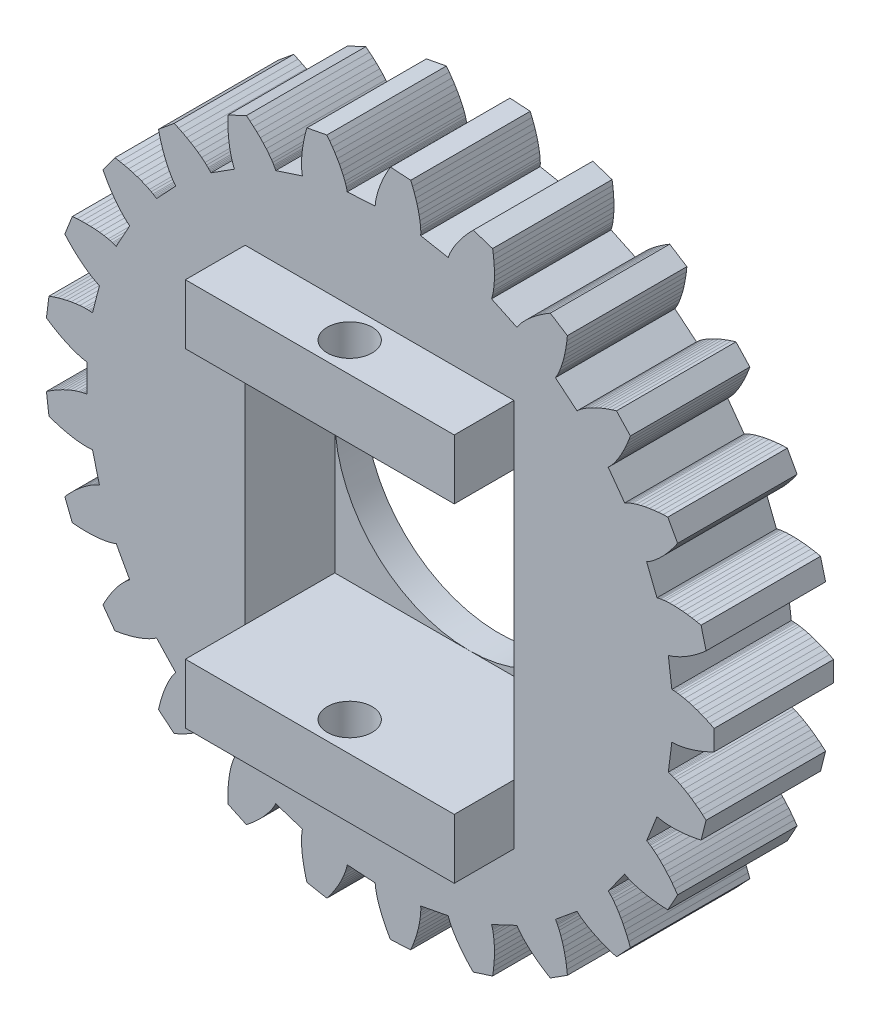
SolidWorks part; units mm, degrees
ref_plane "Front Plane" through (0, 0, 0) normal (0, 0, 1) x (1, 0, 0)
ref_plane "Top Plane" through (0, 0, 0) normal (0, 1, 0) x (1, 0, 0)
ref_plane "Right Plane" through (0, 0, 0) normal (1, 0, 0) x (0, 0, -1)
sketch "Model" plane through (0, 0, 0) normal (0, 0, 1) x (1, 0, 0)
  line L0 (22.5153, 13.4937) -> (22.5501, 13.4944)
  line L1 (22.5501, 13.4944) -> (22.5851, 13.4936)
  line L2 (22.5851, 13.4936) -> (22.6201, 13.4916)
  line L3 (22.6201, 13.4916) -> (22.6552, 13.4888)
  line L4 (22.6552, 13.4888) -> (22.7255, 13.481)
  line L5 (22.7255, 13.481) -> (22.796, 13.4706)
  line L6 (22.796, 13.4706) -> (22.9373, 13.4433)
  line L7 (22.9373, 13.4433) -> (23.079, 13.4085)
  line L8 (23.079, 13.4085) -> (23.221, 13.3669)
  line L9 (23.221, 13.3669) -> (23.363, 13.3191)
  line L10 (23.363, 13.3191) -> (23.5051, 13.2655)
  line L11 (23.5051, 13.2655) -> (23.647, 13.2062)
  line L12 (23.647, 13.2062) -> (23.7888, 13.1416)
  line L13 (23.7888, 13.1416) -> (23.9303, 13.0718)
  line L14 (23.9303, 13.0718) -> (23.9303, 12.3915)
  line L15 (23.9303, 12.3915) -> (23.7888, 12.3217)
  line L16 (23.7888, 12.3217) -> (23.647, 12.257)
  line L17 (23.647, 12.257) -> (23.5051, 12.1978)
  line L18 (23.5051, 12.1978) -> (23.363, 12.1441)
  line L19 (23.363, 12.1441) -> (23.221, 12.0963)
  line L20 (23.221, 12.0963) -> (23.079, 12.0548)
  line L21 (23.079, 12.0548) -> (22.9373, 12.0199)
  line L22 (22.9373, 12.0199) -> (22.796, 11.9927)
  line L23 (22.796, 11.9927) -> (22.7255, 11.9823)
  line L24 (22.7255, 11.9823) -> (22.6552, 11.9745)
  line L25 (22.6552, 11.9745) -> (22.6201, 11.9716)
  line L26 (22.6201, 11.9716) -> (22.5851, 11.9697)
  line L27 (22.5851, 11.9697) -> (22.5501, 11.9688)
  line L28 (22.5501, 11.9688) -> (22.5153, 11.9696)
  line L29 (22.5153, 11.9696) -> (22.3975, 11.0367)
  line L30 (22.3975, 11.0367) -> (22.4314, 11.0287)
  line L31 (22.4314, 11.0287) -> (22.465, 11.0192)
  line L32 (22.465, 11.0192) -> (22.4984, 11.0086)
  line L33 (22.4984, 11.0086) -> (22.5317, 10.9971)
  line L34 (22.5317, 10.9971) -> (22.5978, 10.9721)
  line L35 (22.5978, 10.9721) -> (22.6635, 10.9445)
  line L36 (22.6635, 10.9445) -> (22.7937, 10.8829)
  line L37 (22.7937, 10.8829) -> (22.9223, 10.8139)
  line L38 (22.9223, 10.8139) -> (23.0494, 10.7384)
  line L39 (23.0494, 10.7384) -> (23.1751, 10.6567)
  line L40 (23.1751, 10.6567) -> (23.2994, 10.5694)
  line L41 (23.2994, 10.5694) -> (23.4221, 10.4767)
  line L42 (23.4221, 10.4767) -> (23.5434, 10.3789)
  line L43 (23.5434, 10.3789) -> (23.6631, 10.2761)
  line L44 (23.6631, 10.2761) -> (23.4939, 9.6172)
  line L45 (23.4939, 9.6172) -> (23.3395, 9.5847)
  line L46 (23.3395, 9.5847) -> (23.1861, 9.5574)
  line L47 (23.1861, 9.5574) -> (23.0339, 9.5353)
  line L48 (23.0339, 9.5353) -> (22.8829, 9.5187)
  line L49 (22.8829, 9.5187) -> (22.7334, 9.5077)
  line L50 (22.7334, 9.5077) -> (22.5856, 9.5027)
  line L51 (22.5856, 9.5027) -> (22.4397, 9.5042)
  line L52 (22.4397, 9.5042) -> (22.296, 9.513)
  line L53 (22.296, 9.513) -> (22.2251, 9.5205)
  line L54 (22.2251, 9.5205) -> (22.1551, 9.5304)
  line L55 (22.1551, 9.5304) -> (22.1204, 9.5364)
  line L56 (22.1204, 9.5364) -> (22.086, 9.5432)
  line L57 (22.086, 9.5432) -> (22.0519, 9.551)
  line L58 (22.0519, 9.551) -> (22.0184, 9.5604)
  line L59 (22.0184, 9.5604) -> (21.6723, 8.6861)
  line L60 (21.6723, 8.6861) -> (21.7031, 8.67)
  line L61 (21.7031, 8.67) -> (21.7333, 8.6524)
  line L62 (21.7333, 8.6524) -> (21.7631, 8.6338)
  line L63 (21.7631, 8.6338) -> (21.7925, 8.6145)
  line L64 (21.7925, 8.6145) -> (21.8503, 8.5737)
  line L65 (21.8503, 8.5737) -> (21.9071, 8.5306)
  line L66 (21.9071, 8.5306) -> (22.0178, 8.4387)
  line L67 (22.0178, 8.4387) -> (22.1252, 8.3399)
  line L68 (22.1252, 8.3399) -> (22.2296, 8.2351)
  line L69 (22.2296, 8.2351) -> (22.331, 8.1247)
  line L70 (22.331, 8.1247) -> (22.4297, 8.0093)
  line L71 (22.4297, 8.0093) -> (22.5255, 7.889)
  line L72 (22.5255, 7.889) -> (22.6186, 7.764)
  line L73 (22.6186, 7.764) -> (22.709, 7.6347)
  line L74 (22.709, 7.6347) -> (22.3812, 7.0385)
  line L75 (22.3812, 7.0385) -> (22.2236, 7.0455)
  line L76 (22.2236, 7.0455) -> (22.0683, 7.0572)
  line L77 (22.0683, 7.0572) -> (21.9153, 7.0737)
  line L78 (21.9153, 7.0737) -> (21.765, 7.0951)
  line L79 (21.765, 7.0951) -> (21.6175, 7.1216)
  line L80 (21.6175, 7.1216) -> (21.473, 7.1536)
  line L81 (21.473, 7.1536) -> (21.3321, 7.1913)
  line L82 (21.3321, 7.1913) -> (21.1951, 7.2356)
  line L83 (21.1951, 7.2356) -> (21.1283, 7.2604)
  line L84 (21.1283, 7.2604) -> (21.0629, 7.2874)
  line L85 (21.0629, 7.2874) -> (21.0308, 7.3018)
  line L86 (21.0308, 7.3018) -> (20.9992, 7.317)
  line L87 (20.9992, 7.317) -> (20.9681, 7.3331)
  line L88 (20.9681, 7.3331) -> (20.938, 7.3505)
  line L89 (20.938, 7.3505) -> (20.3853, 6.5898)
  line L90 (20.3853, 6.5898) -> (20.4112, 6.5665)
  line L91 (20.4112, 6.5665) -> (20.4361, 6.5419)
  line L92 (20.4361, 6.5419) -> (20.4602, 6.5165)
  line L93 (20.4602, 6.5165) -> (20.4839, 6.4905)
  line L94 (20.4839, 6.4905) -> (20.5298, 6.4366)
  line L95 (20.5298, 6.4366) -> (20.574, 6.3808)
  line L96 (20.574, 6.3808) -> (20.6584, 6.2642)
  line L97 (20.6584, 6.2642) -> (20.7379, 6.1418)
  line L98 (20.7379, 6.1418) -> (20.8129, 6.0143)
  line L99 (20.8129, 6.0143) -> (20.8838, 5.8822)
  line L100 (20.8838, 5.8822) -> (20.9506, 5.7458)
  line L101 (20.9506, 5.7458) -> (21.0135, 5.6055)
  line L102 (21.0135, 5.6055) -> (21.0726, 5.4613)
  line L103 (21.0726, 5.4613) -> (21.128, 5.3136)
  line L104 (21.128, 5.3136) -> (20.6622, 4.8176)
  line L105 (20.6622, 4.8176) -> (20.5113, 4.8636)
  line L106 (20.5113, 4.8636) -> (20.3638, 4.9136)
  line L107 (20.3638, 4.9136) -> (20.2197, 4.9675)
  line L108 (20.2197, 4.9675) -> (20.0794, 5.0257)
  line L109 (20.0794, 5.0257) -> (19.9432, 5.0881)
  line L110 (19.9432, 5.0881) -> (19.8112, 5.1549)
  line L111 (19.8112, 5.1549) -> (19.6841, 5.2265)
  line L112 (19.6841, 5.2265) -> (19.5624, 5.3035)
  line L113 (19.5624, 5.3035) -> (19.5039, 5.3441)
  line L114 (19.5039, 5.3441) -> (19.4472, 5.3866)
  line L115 (19.4472, 5.3866) -> (19.4197, 5.4085)
  line L116 (19.4197, 5.4085) -> (19.3929, 5.4311)
  line L117 (19.3929, 5.4311) -> (19.3668, 5.4543)
  line L118 (19.3668, 5.4543) -> (19.3419, 5.4787)
  line L119 (19.3419, 5.4787) -> (18.6174, 4.8793)
  line L120 (18.6174, 4.8793) -> (18.6367, 4.8503)
  line L121 (18.6367, 4.8503) -> (18.6547, 4.8204)
  line L122 (18.6547, 4.8204) -> (18.6718, 4.7898)
  line L123 (18.6718, 4.7898) -> (18.6882, 4.7586)
  line L124 (18.6882, 4.7586) -> (18.7193, 4.6951)
  line L125 (18.7193, 4.6951) -> (18.7483, 4.63)
  line L126 (18.7483, 4.63) -> (18.801, 4.496)
  line L127 (18.801, 4.496) -> (18.8476, 4.3577)
  line L128 (18.8476, 4.3577) -> (18.8885, 4.2156)
  line L129 (18.8885, 4.2156) -> (18.9243, 4.07)
  line L130 (18.9243, 4.07) -> (18.9551, 3.9213)
  line L131 (18.9551, 3.9213) -> (18.9811, 3.7697)
  line L132 (18.9811, 3.7697) -> (19.0025, 3.6154)
  line L133 (19.0025, 3.6154) -> (19.0194, 3.4586)
  line L134 (19.0194, 3.4586) -> (18.445, 3.094)
  line L135 (18.445, 3.094) -> (18.3102, 3.1761)
  line L136 (18.3102, 3.1761) -> (18.1797, 3.2611)
  line L137 (18.1797, 3.2611) -> (18.0536, 3.3493)
  line L138 (18.0536, 3.3493) -> (17.9322, 3.4404)
  line L139 (17.9322, 3.4404) -> (17.8157, 3.5348)
  line L140 (17.8157, 3.5348) -> (17.7045, 3.6323)
  line L141 (17.7045, 3.6323) -> (17.5992, 3.7333)
  line L142 (17.5992, 3.7333) -> (17.5004, 3.8381)
  line L143 (17.5004, 3.8381) -> (17.4539, 3.892)
  line L144 (17.4539, 3.892) -> (17.4096, 3.9472)
  line L145 (17.4096, 3.9472) -> (17.3884, 3.9753)
  line L146 (17.3884, 3.9753) -> (17.368, 4.0038)
  line L147 (17.368, 4.0038) -> (17.3486, 4.0329)
  line L148 (17.3486, 4.0329) -> (17.3305, 4.0626)
  line L149 (17.3305, 4.0626) -> (16.4797, 3.6623)
  line L150 (16.4797, 3.6623) -> (16.4912, 3.6294)
  line L151 (16.4912, 3.6294) -> (16.5012, 3.5959)
  line L152 (16.5012, 3.5959) -> (16.5101, 3.562)
  line L153 (16.5101, 3.562) -> (16.5183, 3.5278)
  line L154 (16.5183, 3.5278) -> (16.5326, 3.4585)
  line L155 (16.5326, 3.4585) -> (16.5445, 3.3882)
  line L156 (16.5445, 3.3882) -> (16.5622, 3.2454)
  line L157 (16.5622, 3.2454) -> (16.5729, 3.0998)
  line L158 (16.5729, 3.0998) -> (16.5772, 2.952)
  line L159 (16.5772, 2.952) -> (16.5756, 2.8021)
  line L160 (16.5756, 2.8021) -> (16.5685, 2.6504)
  line L161 (16.5685, 2.6504) -> (16.556, 2.4971)
  line L162 (16.556, 2.4971) -> (16.5384, 2.3423)
  line L163 (16.5384, 2.3423) -> (16.5157, 2.1862)
  line L164 (16.5157, 2.1862) -> (15.8687, 1.9759)
  line L165 (15.8687, 1.9759) -> (15.7586, 2.0889)
  line L166 (15.7586, 2.0889) -> (15.6533, 2.2038)
  line L167 (15.6533, 2.2038) -> (15.5531, 2.3205)
  line L168 (15.5531, 2.3205) -> (15.4582, 2.439)
  line L169 (15.4582, 2.439) -> (15.3688, 2.5593)
  line L170 (15.3688, 2.5593) -> (15.2854, 2.6815)
  line L171 (15.2854, 2.6815) -> (15.2085, 2.8055)
  line L172 (15.2085, 2.8055) -> (15.1389, 2.9315)
  line L173 (15.1389, 2.9315) -> (15.1072, 2.9954)
  line L174 (15.1072, 2.9954) -> (15.078, 3.0598)
  line L175 (15.078, 3.0598) -> (15.0645, 3.0923)
  line L176 (15.0645, 3.0923) -> (15.0519, 3.125)
  line L177 (15.0519, 3.125) -> (15.0402, 3.158)
  line L178 (15.0402, 3.158) -> (15.0302, 3.1913)
  line L179 (15.0302, 3.1913) -> (14.1065, 3.0151)
  line L180 (14.1065, 3.0151) -> (14.1095, 2.9804)
  line L181 (14.1095, 2.9804) -> (14.1108, 2.9455)
  line L182 (14.1108, 2.9455) -> (14.111, 2.9104)
  line L183 (14.111, 2.9104) -> (14.1104, 2.8752)
  line L184 (14.1104, 2.8752) -> (14.107, 2.8046)
  line L185 (14.107, 2.8046) -> (14.1011, 2.7336)
  line L186 (14.1011, 2.7336) -> (14.0827, 2.5908)
  line L187 (14.0827, 2.5908) -> (14.0569, 2.4471)
  line L188 (14.0569, 2.4471) -> (14.0243, 2.3029)
  line L189 (14.0243, 2.3029) -> (13.9855, 2.1581)
  line L190 (13.9855, 2.1581) -> (13.9409, 2.0129)
  line L191 (13.9409, 2.0129) -> (13.8907, 1.8675)
  line L192 (13.8907, 1.8675) -> (13.8351, 1.722)
  line L193 (13.8351, 1.722) -> (13.7743, 1.5764)
  line L194 (13.7743, 1.5764) -> (13.0953, 1.5337)
  line L195 (13.0953, 1.5337) -> (13.0168, 1.6705)
  line L196 (13.0168, 1.6705) -> (12.9434, 1.808)
  line L197 (12.9434, 1.808) -> (12.8753, 1.9459)
  line L198 (12.8753, 1.9459) -> (12.8128, 2.0843)
  line L199 (12.8128, 2.0843) -> (12.7562, 2.2231)
  line L200 (12.7562, 2.2231) -> (12.7058, 2.3621)
  line L201 (12.7058, 2.3621) -> (12.6622, 2.5014)
  line L202 (12.6622, 2.5014) -> (12.6261, 2.6408)
  line L203 (12.6261, 2.6408) -> (12.6113, 2.7105)
  line L204 (12.6113, 2.7105) -> (12.599, 2.7801)
  line L205 (12.599, 2.7801) -> (12.594, 2.815)
  line L206 (12.594, 2.815) -> (12.5899, 2.8498)
  line L207 (12.5899, 2.8498) -> (12.5868, 2.8846)
  line L208 (12.5868, 2.8846) -> (12.5854, 2.9194)
  line L209 (12.5854, 2.9194) -> (11.6469, 2.9784)
  line L210 (11.6469, 2.9784) -> (11.6411, 2.9441)
  line L211 (11.6411, 2.9441) -> (11.6337, 2.91)
  line L212 (11.6337, 2.91) -> (11.6253, 2.8759)
  line L213 (11.6253, 2.8759) -> (11.6159, 2.842)
  line L214 (11.6159, 2.842) -> (11.595, 2.7744)
  line L215 (11.595, 2.7744) -> (11.5716, 2.7071)
  line L216 (11.5716, 2.7071) -> (11.5184, 2.5733)
  line L217 (11.5184, 2.5733) -> (11.4576, 2.4407)
  line L218 (11.4576, 2.4407) -> (11.3902, 2.309)
  line L219 (11.3902, 2.309) -> (11.3166, 2.1784)
  line L220 (11.3166, 2.1784) -> (11.2372, 2.049)
  line L221 (11.2372, 2.049) -> (11.1525, 1.9206)
  line L222 (11.1525, 1.9206) -> (11.0624, 1.7935)
  line L223 (11.0624, 1.7935) -> (10.9673, 1.6676)
  line L224 (10.9673, 1.6676) -> (10.2991, 1.7951)
  line L225 (10.2991, 1.7951) -> (10.257, 1.9471)
  line L226 (10.257, 1.9471) -> (10.2201, 2.0985)
  line L227 (10.2201, 2.0985) -> (10.1885, 2.249)
  line L228 (10.1885, 2.249) -> (10.1624, 2.3986)
  line L229 (10.1624, 2.3986) -> (10.1421, 2.5471)
  line L230 (10.1421, 2.5471) -> (10.1278, 2.6943)
  line L231 (10.1278, 2.6943) -> (10.1202, 2.8401)
  line L232 (10.1202, 2.8401) -> (10.1199, 2.984)
  line L233 (10.1199, 2.984) -> (10.1229, 3.0552)
  line L234 (10.1229, 3.0552) -> (10.1284, 3.1258)
  line L235 (10.1284, 3.1258) -> (10.1322, 3.1607)
  line L236 (10.1322, 3.1607) -> (10.1368, 3.1955)
  line L237 (10.1368, 3.1955) -> (10.1425, 3.23)
  line L238 (10.1425, 3.23) -> (10.1498, 3.264)
  line L239 (10.1498, 3.264) -> (9.2555, 3.5546)
  line L240 (9.2555, 3.5546) -> (9.2413, 3.5228)
  line L241 (9.2413, 3.5228) -> (9.2257, 3.4916)
  line L242 (9.2257, 3.4916) -> (9.209, 3.4607)
  line L243 (9.209, 3.4607) -> (9.1915, 3.4302)
  line L244 (9.1915, 3.4302) -> (9.1545, 3.3699)
  line L245 (9.1545, 3.3699) -> (9.1151, 3.3105)
  line L246 (9.1151, 3.3105) -> (9.0302, 3.1942)
  line L247 (9.0302, 3.1942) -> (8.9384, 3.0808)
  line L248 (8.9384, 3.0808) -> (8.8403, 2.9701)
  line L249 (8.8403, 2.9701) -> (8.7366, 2.8619)
  line L250 (8.7366, 2.8619) -> (8.6275, 2.7562)
  line L251 (8.6275, 2.7562) -> (8.5135, 2.653)
  line L252 (8.5135, 2.653) -> (8.3947, 2.5522)
  line L253 (8.3947, 2.5522) -> (8.2713, 2.4539)
  line L254 (8.2713, 2.4539) -> (7.6557, 2.7436)
  line L255 (7.6557, 2.7436) -> (7.6528, 2.9013)
  line L256 (7.6528, 2.9013) -> (7.6547, 3.0571)
  line L257 (7.6547, 3.0571) -> (7.6615, 3.2108)
  line L258 (7.6615, 3.2108) -> (7.6734, 3.3622)
  line L259 (7.6734, 3.3622) -> (7.6906, 3.5111)
  line L260 (7.6906, 3.5111) -> (7.7135, 3.6572)
  line L261 (7.7135, 3.6572) -> (7.7423, 3.8003)
  line L262 (7.7423, 3.8003) -> (7.7778, 3.9398)
  line L263 (7.7778, 3.9398) -> (7.7984, 4.008)
  line L264 (7.7984, 4.008) -> (7.8213, 4.0749)
  line L265 (7.8213, 4.0749) -> (7.8337, 4.1079)
  line L266 (7.8337, 4.1079) -> (7.8468, 4.1404)
  line L267 (7.8468, 4.1404) -> (7.8609, 4.1724)
  line L268 (7.8609, 4.1724) -> (7.8764, 4.2036)
  line L269 (7.8764, 4.2036) -> (7.0825, 4.7074)
  line L270 (7.0825, 4.7074) -> (7.0608, 4.6801)
  line L271 (7.0608, 4.6801) -> (7.0379, 4.6537)
  line L272 (7.0379, 4.6537) -> (7.0141, 4.628)
  line L273 (7.0141, 4.628) -> (6.9896, 4.6028)
  line L274 (6.9896, 4.6028) -> (6.9387, 4.5536)
  line L275 (6.9387, 4.5536) -> (6.8858, 4.5059)
  line L276 (6.8858, 4.5059) -> (6.7746, 4.4144)
  line L277 (6.7746, 4.4144) -> (6.6575, 4.3274)
  line L278 (6.6575, 4.3274) -> (6.535, 4.2445)
  line L279 (6.535, 4.2445) -> (6.4076, 4.1655)
  line L280 (6.4076, 4.1655) -> (6.2757, 4.0903)
  line L281 (6.2757, 4.0903) -> (6.1395, 4.0186)
  line L282 (6.1395, 4.0186) -> (5.9994, 3.9506)
  line L283 (5.9994, 3.9506) -> (5.8554, 3.8861)
  line L284 (5.8554, 3.8861) -> (5.3312, 4.3197)
  line L285 (5.3312, 4.3197) -> (5.3676, 4.4732)
  line L286 (5.3676, 4.4732) -> (5.4082, 4.6237)
  line L287 (5.4082, 4.6237) -> (5.453, 4.7708)
  line L288 (5.453, 4.7708) -> (5.5022, 4.9145)
  line L289 (5.5022, 4.9145) -> (5.556, 5.0544)
  line L290 (5.556, 5.0544) -> (5.6144, 5.1903)
  line L291 (5.6144, 5.1903) -> (5.6779, 5.3217)
  line L292 (5.6779, 5.3217) -> (5.747, 5.4479)
  line L293 (5.747, 5.4479) -> (5.7839, 5.5089)
  line L294 (5.7839, 5.5089) -> (5.8227, 5.5681)
  line L295 (5.8227, 5.5681) -> (5.8429, 5.5969)
  line L296 (5.8429, 5.5969) -> (5.8637, 5.6251)
  line L297 (5.8637, 5.6251) -> (5.8853, 5.6526)
  line L298 (5.8853, 5.6526) -> (5.9081, 5.6789)
  line L299 (5.9081, 5.6789) -> (5.2644, 6.3644)
  line L300 (5.2644, 6.3644) -> (5.2367, 6.3433)
  line L301 (5.2367, 6.3433) -> (5.2079, 6.3235)
  line L302 (5.2079, 6.3235) -> (5.1784, 6.3045)
  line L303 (5.1784, 6.3045) -> (5.1484, 6.2862)
  line L304 (5.1484, 6.2862) -> (5.0869, 6.2512)
  line L305 (5.0869, 6.2512) -> (5.0238, 6.2181)
  line L306 (5.0238, 6.2181) -> (4.8934, 6.1571)
  line L307 (4.8934, 6.1571) -> (4.7583, 6.102)
  line L308 (4.7583, 6.102) -> (4.619, 6.0522)
  line L309 (4.619, 6.0522) -> (4.476, 6.0074)
  line L310 (4.476, 6.0074) -> (4.3295, 5.9673)
  line L311 (4.3295, 5.9673) -> (4.1798, 5.9318)
  line L312 (4.1798, 5.9318) -> (4.0272, 5.9007)
  line L313 (4.0272, 5.9007) -> (3.8717, 5.874)
  line L314 (3.8717, 5.874) -> (3.4718, 6.4244)
  line L315 (3.4718, 6.4244) -> (3.5452, 6.5641)
  line L316 (3.5452, 6.5641) -> (3.6219, 6.6996)
  line L317 (3.6219, 6.6996) -> (3.7019, 6.831)
  line L318 (3.7019, 6.831) -> (3.7853, 6.9579)
  line L319 (3.7853, 6.9579) -> (3.8721, 7.0801)
  line L320 (3.8721, 7.0801) -> (3.9625, 7.1972)
  line L321 (3.9625, 7.1972) -> (4.0567, 7.3086)
  line L322 (4.0567, 7.3086) -> (4.1551, 7.4138)
  line L323 (4.1551, 7.4138) -> (4.206, 7.4636)
  line L324 (4.206, 7.4636) -> (4.2583, 7.5113)
  line L325 (4.2583, 7.5113) -> (4.285, 7.5342)
  line L326 (4.285, 7.5342) -> (4.3122, 7.5563)
  line L327 (4.3122, 7.5563) -> (4.3399, 7.5776)
  line L328 (4.3399, 7.5776) -> (4.3685, 7.5975)
  line L329 (4.3685, 7.5975) -> (3.9155, 8.4215)
  line L330 (3.9155, 8.4215) -> (3.8834, 8.4079)
  line L331 (3.8834, 8.4079) -> (3.8506, 8.3959)
  line L332 (3.8506, 8.3959) -> (3.8174, 8.3848)
  line L333 (3.8174, 8.3848) -> (3.7837, 8.3745)
  line L334 (3.7837, 8.3745) -> (3.7154, 8.3559)
  line L335 (3.7154, 8.3559) -> (3.6461, 8.3396)
  line L336 (3.6461, 8.3396) -> (3.5046, 8.3129)
  line L337 (3.5046, 8.3129) -> (3.36, 8.2932)
  line L338 (3.36, 8.2932) -> (3.2127, 8.2796)
  line L339 (3.2127, 8.2796) -> (3.0631, 8.2717)
  line L340 (3.0631, 8.2717) -> (2.9112, 8.2693)
  line L341 (2.9112, 8.2693) -> (2.7574, 8.2721)
  line L342 (2.7574, 8.2721) -> (2.6018, 8.28)
  line L343 (2.6018, 8.28) -> (2.4446, 8.2928)
  line L344 (2.4446, 8.2928) -> (2.1941, 8.9254)
  line L345 (2.1941, 8.9254) -> (2.3, 9.0424)
  line L346 (2.3, 9.0424) -> (2.408, 9.1547)
  line L347 (2.408, 9.1547) -> (2.5182, 9.262)
  line L348 (2.5182, 9.262) -> (2.6305, 9.3642)
  line L349 (2.6305, 9.3642) -> (2.745, 9.4609)
  line L350 (2.745, 9.4609) -> (2.8617, 9.5518)
  line L351 (2.8617, 9.5518) -> (2.9806, 9.6364)
  line L352 (2.9806, 9.6364) -> (3.102, 9.7138)
  line L353 (3.102, 9.7138) -> (3.1637, 9.7494)
  line L354 (3.1637, 9.7494) -> (3.2262, 9.7825)
  line L355 (3.2262, 9.7825) -> (3.2578, 9.7981)
  line L356 (3.2578, 9.7981) -> (3.2897, 9.8128)
  line L357 (3.2897, 9.8128) -> (3.3218, 9.8265)
  line L358 (3.3218, 9.8265) -> (3.3544, 9.8386)
  line L359 (3.3544, 9.8386) -> (3.1206, 10.7493)
  line L360 (3.1206, 10.7493) -> (3.0862, 10.7442)
  line L361 (3.0862, 10.7442) -> (3.0514, 10.7407)
  line L362 (3.0514, 10.7407) -> (3.0164, 10.7383)
  line L363 (3.0164, 10.7383) -> (2.9813, 10.7367)
  line L364 (2.9813, 10.7367) -> (2.9105, 10.7356)
  line L365 (2.9105, 10.7356) -> (2.8393, 10.7371)
  line L366 (2.8393, 10.7371) -> (2.6956, 10.7464)
  line L367 (2.6956, 10.7464) -> (2.5506, 10.7632)
  line L368 (2.5506, 10.7632) -> (2.4046, 10.7867)
  line L369 (2.4046, 10.7867) -> (2.2577, 10.8163)
  line L370 (2.2577, 10.8163) -> (2.11, 10.8517)
  line L371 (2.11, 10.8517) -> (1.9618, 10.8927)
  line L372 (1.9618, 10.8927) -> (1.813, 10.9391)
  line L373 (1.813, 10.9391) -> (1.6639, 10.9906)
  line L374 (1.6639, 10.9906) -> (1.5786, 11.6655)
  line L375 (1.5786, 11.6655) -> (1.7103, 11.7525)
  line L376 (1.7103, 11.7525) -> (1.8428, 11.8344)
  line L377 (1.8428, 11.8344) -> (1.9762, 11.911)
  line L378 (1.9762, 11.911) -> (2.1104, 11.982)
  line L379 (2.1104, 11.982) -> (2.2454, 12.0472)
  line L380 (2.2454, 12.0472) -> (2.381, 12.1063)
  line L381 (2.381, 12.1063) -> (2.5172, 12.1586)
  line L382 (2.5172, 12.1586) -> (2.654, 12.2034)
  line L383 (2.654, 12.2034) -> (2.7227, 12.2225)
  line L384 (2.7227, 12.2225) -> (2.7915, 12.2391)
  line L385 (2.7915, 12.2391) -> (2.8259, 12.2463)
  line L386 (2.8259, 12.2463) -> (2.8604, 12.2526)
  line L387 (2.8604, 12.2526) -> (2.8949, 12.2578)
  line L388 (2.8949, 12.2578) -> (2.9296, 12.2615)
  line L389 (2.9296, 12.2615) -> (2.9296, 13.2018)
  line L390 (2.9296, 13.2018) -> (2.8949, 13.2054)
  line L391 (2.8949, 13.2054) -> (2.8604, 13.2107)
  line L392 (2.8604, 13.2107) -> (2.8259, 13.217)
  line L393 (2.8259, 13.217) -> (2.7915, 13.2242)
  line L394 (2.7915, 13.2242) -> (2.7227, 13.2408)
  line L395 (2.7227, 13.2408) -> (2.654, 13.2599)
  line L396 (2.654, 13.2599) -> (2.5172, 13.3047)
  line L397 (2.5172, 13.3047) -> (2.381, 13.357)
  line L398 (2.381, 13.357) -> (2.2454, 13.416)
  line L399 (2.2454, 13.416) -> (2.1104, 13.4812)
  line L400 (2.1104, 13.4812) -> (1.9762, 13.5523)
  line L401 (1.9762, 13.5523) -> (1.8428, 13.6289)
  line L402 (1.8428, 13.6289) -> (1.7103, 13.7107)
  line L403 (1.7103, 13.7107) -> (1.5786, 13.7977)
  line L404 (1.5786, 13.7977) -> (1.6639, 14.4727)
  line L405 (1.6639, 14.4727) -> (1.813, 14.5242)
  line L406 (1.813, 14.5242) -> (1.9618, 14.5705)
  line L407 (1.9618, 14.5705) -> (2.11, 14.6115)
  line L408 (2.11, 14.6115) -> (2.2577, 14.647)
  line L409 (2.2577, 14.647) -> (2.4046, 14.6766)
  line L410 (2.4046, 14.6766) -> (2.5506, 14.7)
  line L411 (2.5506, 14.7) -> (2.6956, 14.7168)
  line L412 (2.6956, 14.7168) -> (2.8393, 14.7261)
  line L413 (2.8393, 14.7261) -> (2.9105, 14.7276)
  line L414 (2.9105, 14.7276) -> (2.9813, 14.7266)
  line L415 (2.9813, 14.7266) -> (3.0164, 14.725)
  line L416 (3.0164, 14.725) -> (3.0514, 14.7225)
  line L417 (3.0514, 14.7225) -> (3.0862, 14.719)
  line L418 (3.0862, 14.719) -> (3.1206, 14.7139)
  line L419 (3.1206, 14.7139) -> (3.3544, 15.6247)
  line L420 (3.3544, 15.6247) -> (3.3218, 15.6368)
  line L421 (3.3218, 15.6368) -> (3.2897, 15.6505)
  line L422 (3.2897, 15.6505) -> (3.2578, 15.6652)
  line L423 (3.2578, 15.6652) -> (3.2262, 15.6807)
  line L424 (3.2262, 15.6807) -> (3.1637, 15.7139)
  line L425 (3.1637, 15.7139) -> (3.102, 15.7495)
  line L426 (3.102, 15.7495) -> (2.9806, 15.8269)
  line L427 (2.9806, 15.8269) -> (2.8617, 15.9114)
  line L428 (2.8617, 15.9114) -> (2.745, 16.0023)
  line L429 (2.745, 16.0023) -> (2.6305, 16.0991)
  line L430 (2.6305, 16.0991) -> (2.5182, 16.2013)
  line L431 (2.5182, 16.2013) -> (2.408, 16.3086)
  line L432 (2.408, 16.3086) -> (2.3, 16.4209)
  line L433 (2.3, 16.4209) -> (2.1941, 16.5379)
  line L434 (2.1941, 16.5379) -> (2.4446, 17.1704)
  line L435 (2.4446, 17.1704) -> (2.6018, 17.1832)
  line L436 (2.6018, 17.1832) -> (2.7574, 17.1911)
  line L437 (2.7574, 17.1911) -> (2.9112, 17.1939)
  line L438 (2.9112, 17.1939) -> (3.0631, 17.1915)
  line L439 (3.0631, 17.1915) -> (3.2127, 17.1837)
  line L440 (3.2127, 17.1837) -> (3.36, 17.1701)
  line L441 (3.36, 17.1701) -> (3.5046, 17.1503)
  line L442 (3.5046, 17.1503) -> (3.6461, 17.1236)
  line L443 (3.6461, 17.1236) -> (3.7154, 17.1073)
  line L444 (3.7154, 17.1073) -> (3.7837, 17.0887)
  line L445 (3.7837, 17.0887) -> (3.8174, 17.0784)
  line L446 (3.8174, 17.0784) -> (3.8506, 17.0674)
  line L447 (3.8506, 17.0674) -> (3.8834, 17.0553)
  line L448 (3.8834, 17.0553) -> (3.9155, 17.0418)
  line L449 (3.9155, 17.0418) -> (4.3685, 17.8658)
  line L450 (4.3685, 17.8658) -> (4.3399, 17.8857)
  line L451 (4.3399, 17.8857) -> (4.3122, 17.9069)
  line L452 (4.3122, 17.9069) -> (4.285, 17.9291)
  line L453 (4.285, 17.9291) -> (4.2583, 17.952)
  line L454 (4.2583, 17.952) -> (4.206, 17.9996)
  line L455 (4.206, 17.9996) -> (4.1551, 18.0495)
  line L456 (4.1551, 18.0495) -> (4.0567, 18.1546)
  line L457 (4.0567, 18.1546) -> (3.9625, 18.2661)
  line L458 (3.9625, 18.2661) -> (3.8721, 18.3831)
  line L459 (3.8721, 18.3831) -> (3.7853, 18.5053)
  line L460 (3.7853, 18.5053) -> (3.7019, 18.6322)
  line L461 (3.7019, 18.6322) -> (3.6219, 18.7636)
  line L462 (3.6219, 18.7636) -> (3.5452, 18.8992)
  line L463 (3.5452, 18.8992) -> (3.4718, 19.0388)
  line L464 (3.4718, 19.0388) -> (3.8717, 19.5892)
  line L465 (3.8717, 19.5892) -> (4.0272, 19.5626)
  line L466 (4.0272, 19.5626) -> (4.1798, 19.5315)
  line L467 (4.1798, 19.5315) -> (4.3295, 19.496)
  line L468 (4.3295, 19.496) -> (4.476, 19.4559)
  line L469 (4.476, 19.4559) -> (4.619, 19.4111)
  line L470 (4.619, 19.4111) -> (4.7583, 19.3613)
  line L471 (4.7583, 19.3613) -> (4.8934, 19.3062)
  line L472 (4.8934, 19.3062) -> (5.0238, 19.2451)
  line L473 (5.0238, 19.2451) -> (5.0869, 19.2121)
  line L474 (5.0869, 19.2121) -> (5.1484, 19.1771)
  line L475 (5.1484, 19.1771) -> (5.1784, 19.1588)
  line L476 (5.1784, 19.1588) -> (5.2079, 19.1398)
  line L477 (5.2079, 19.1398) -> (5.2367, 19.1199)
  line L478 (5.2367, 19.1199) -> (5.2644, 19.0989)
  line L479 (5.2644, 19.0989) -> (5.9081, 19.7843)
  line L480 (5.9081, 19.7843) -> (5.8853, 19.8107)
  line L481 (5.8853, 19.8107) -> (5.8637, 19.8381)
  line L482 (5.8637, 19.8381) -> (5.8429, 19.8664)
  line L483 (5.8429, 19.8664) -> (5.8227, 19.8952)
  line L484 (5.8227, 19.8952) -> (5.7839, 19.9544)
  line L485 (5.7839, 19.9544) -> (5.747, 20.0153)
  line L486 (5.747, 20.0153) -> (5.6779, 20.1416)
  line L487 (5.6779, 20.1416) -> (5.6144, 20.273)
  line L488 (5.6144, 20.273) -> (5.556, 20.4089)
  line L489 (5.556, 20.4089) -> (5.5022, 20.5488)
  line L490 (5.5022, 20.5488) -> (5.453, 20.6925)
  line L491 (5.453, 20.6925) -> (5.4082, 20.8396)
  line L492 (5.4082, 20.8396) -> (5.3676, 20.99)
  line L493 (5.3676, 20.99) -> (5.3312, 21.1435)
  line L494 (5.3312, 21.1435) -> (5.8554, 21.5772)
  line L495 (5.8554, 21.5772) -> (5.9994, 21.5127)
  line L496 (5.9994, 21.5127) -> (6.1395, 21.4446)
  line L497 (6.1395, 21.4446) -> (6.2757, 21.373)
  line L498 (6.2757, 21.373) -> (6.4076, 21.2977)
  line L499 (6.4076, 21.2977) -> (6.535, 21.2188)
  line L500 (6.535, 21.2188) -> (6.6575, 21.1359)
  line L501 (6.6575, 21.1359) -> (6.7746, 21.0489)
  line L502 (6.7746, 21.0489) -> (6.8858, 20.9574)
  line L503 (6.8858, 20.9574) -> (6.9387, 20.9097)
  line L504 (6.9387, 20.9097) -> (6.9896, 20.8605)
  line L505 (6.9896, 20.8605) -> (7.0141, 20.8352)
  line L506 (7.0141, 20.8352) -> (7.0379, 20.8095)
  line L507 (7.0379, 20.8095) -> (7.0608, 20.7831)
  line L508 (7.0608, 20.7831) -> (7.0825, 20.7559)
  line L509 (7.0825, 20.7559) -> (7.8764, 21.2597)
  line L510 (7.8764, 21.2597) -> (7.8609, 21.2909)
  line L511 (7.8609, 21.2909) -> (7.8468, 21.3229)
  line L512 (7.8468, 21.3229) -> (7.8337, 21.3554)
  line L513 (7.8337, 21.3554) -> (7.8213, 21.3883)
  line L514 (7.8213, 21.3883) -> (7.7984, 21.4553)
  line L515 (7.7984, 21.4553) -> (7.7778, 21.5235)
  line L516 (7.7778, 21.5235) -> (7.7423, 21.663)
  line L517 (7.7423, 21.663) -> (7.7135, 21.806)
  line L518 (7.7135, 21.806) -> (7.6906, 21.9522)
  line L519 (7.6906, 21.9522) -> (7.6734, 22.1011)
  line L520 (7.6734, 22.1011) -> (7.6615, 22.2525)
  line L521 (7.6615, 22.2525) -> (7.6547, 22.4061)
  line L522 (7.6547, 22.4061) -> (7.6528, 22.5619)
  line L523 (7.6528, 22.5619) -> (7.6557, 22.7196)
  line L524 (7.6557, 22.7196) -> (8.2713, 23.0093)
  line L525 (8.2713, 23.0093) -> (8.3947, 22.911)
  line L526 (8.3947, 22.911) -> (8.5135, 22.8103)
  line L527 (8.5135, 22.8103) -> (8.6275, 22.707)
  line L528 (8.6275, 22.707) -> (8.7366, 22.6013)
  line L529 (8.7366, 22.6013) -> (8.8403, 22.4932)
  line L530 (8.8403, 22.4932) -> (8.9384, 22.3824)
  line L531 (8.9384, 22.3824) -> (9.0302, 22.269)
  line L532 (9.0302, 22.269) -> (9.1151, 22.1527)
  line L533 (9.1151, 22.1527) -> (9.1545, 22.0934)
  line L534 (9.1545, 22.0934) -> (9.1915, 22.0331)
  line L535 (9.1915, 22.0331) -> (9.209, 22.0026)
  line L536 (9.209, 22.0026) -> (9.2257, 21.9717)
  line L537 (9.2257, 21.9717) -> (9.2413, 21.9405)
  line L538 (9.2413, 21.9405) -> (9.2555, 21.9086)
  line L539 (9.2555, 21.9086) -> (10.1498, 22.1992)
  line L540 (10.1498, 22.1992) -> (10.1425, 22.2333)
  line L541 (10.1425, 22.2333) -> (10.1368, 22.2677)
  line L542 (10.1368, 22.2677) -> (10.1322, 22.3025)
  line L543 (10.1322, 22.3025) -> (10.1284, 22.3375)
  line L544 (10.1284, 22.3375) -> (10.1229, 22.408)
  line L545 (10.1229, 22.408) -> (10.1199, 22.4792)
  line L546 (10.1199, 22.4792) -> (10.1202, 22.6232)
  line L547 (10.1202, 22.6232) -> (10.1278, 22.7689)
  line L548 (10.1278, 22.7689) -> (10.1421, 22.9161)
  line L549 (10.1421, 22.9161) -> (10.1624, 23.0646)
  line L550 (10.1624, 23.0646) -> (10.1885, 23.2142)
  line L551 (10.1885, 23.2142) -> (10.2201, 23.3648)
  line L552 (10.2201, 23.3648) -> (10.257, 23.5161)
  line L553 (10.257, 23.5161) -> (10.2991, 23.6682)
  line L554 (10.2991, 23.6682) -> (10.9673, 23.7957)
  line L555 (10.9673, 23.7957) -> (11.0624, 23.6698)
  line L556 (11.0624, 23.6698) -> (11.1525, 23.5426)
  line L557 (11.1525, 23.5426) -> (11.2372, 23.4143)
  line L558 (11.2372, 23.4143) -> (11.3166, 23.2848)
  line L559 (11.3166, 23.2848) -> (11.3902, 23.1542)
  line L560 (11.3902, 23.1542) -> (11.4576, 23.0226)
  line L561 (11.4576, 23.0226) -> (11.5184, 22.8899)
  line L562 (11.5184, 22.8899) -> (11.5716, 22.7562)
  line L563 (11.5716, 22.7562) -> (11.595, 22.6889)
  line L564 (11.595, 22.6889) -> (11.6159, 22.6213)
  line L565 (11.6159, 22.6213) -> (11.6253, 22.5873)
  line L566 (11.6253, 22.5873) -> (11.6337, 22.5533)
  line L567 (11.6337, 22.5533) -> (11.6411, 22.5191)
  line L568 (11.6411, 22.5191) -> (11.6469, 22.4848)
  line L569 (11.6469, 22.4848) -> (12.5854, 22.5439)
  line L570 (12.5854, 22.5439) -> (12.5868, 22.5786)
  line L571 (12.5868, 22.5786) -> (12.5899, 22.6135)
  line L572 (12.5899, 22.6135) -> (12.594, 22.6483)
  line L573 (12.594, 22.6483) -> (12.599, 22.6831)
  line L574 (12.599, 22.6831) -> (12.6113, 22.7528)
  line L575 (12.6113, 22.7528) -> (12.6261, 22.8225)
  line L576 (12.6261, 22.8225) -> (12.6622, 22.9619)
  line L577 (12.6622, 22.9619) -> (12.7058, 23.1011)
  line L578 (12.7058, 23.1011) -> (12.7562, 23.2402)
  line L579 (12.7562, 23.2402) -> (12.8128, 23.3789)
  line L580 (12.8128, 23.3789) -> (12.8753, 23.5174)
  line L581 (12.8753, 23.5174) -> (12.9434, 23.6553)
  line L582 (12.9434, 23.6553) -> (13.0168, 23.7927)
  line L583 (13.0168, 23.7927) -> (13.0953, 23.9296)
  line L584 (13.0953, 23.9296) -> (13.7743, 23.8868)
  line L585 (13.7743, 23.8868) -> (13.8351, 23.7412)
  line L586 (13.8351, 23.7412) -> (13.8907, 23.5957)
  line L587 (13.8907, 23.5957) -> (13.9409, 23.4503)
  line L588 (13.9409, 23.4503) -> (13.9855, 23.3052)
  line L589 (13.9855, 23.3052) -> (14.0243, 23.1604)
  line L590 (14.0243, 23.1604) -> (14.0569, 23.0161)
  line L591 (14.0569, 23.0161) -> (14.0827, 22.8725)
  line L592 (14.0827, 22.8725) -> (14.1011, 22.7297)
  line L593 (14.1011, 22.7297) -> (14.107, 22.6587)
  line L594 (14.107, 22.6587) -> (14.1104, 22.588)
  line L595 (14.1104, 22.588) -> (14.111, 22.5528)
  line L596 (14.111, 22.5528) -> (14.1108, 22.5178)
  line L597 (14.1108, 22.5178) -> (14.1095, 22.4828)
  line L598 (14.1095, 22.4828) -> (14.1065, 22.4482)
  line L599 (14.1065, 22.4482) -> (15.0302, 22.272)
  line L600 (15.0302, 22.272) -> (15.0402, 22.3053)
  line L601 (15.0402, 22.3053) -> (15.0519, 22.3382)
  line L602 (15.0519, 22.3382) -> (15.0645, 22.3709)
  line L603 (15.0645, 22.3709) -> (15.078, 22.4034)
  line L604 (15.078, 22.4034) -> (15.1072, 22.4679)
  line L605 (15.1072, 22.4679) -> (15.1389, 22.5317)
  line L606 (15.1389, 22.5317) -> (15.2085, 22.6577)
  line L607 (15.2085, 22.6577) -> (15.2854, 22.7818)
  line L608 (15.2854, 22.7818) -> (15.3688, 22.9039)
  line L609 (15.3688, 22.9039) -> (15.4582, 23.0242)
  line L610 (15.4582, 23.0242) -> (15.5531, 23.1428)
  line L611 (15.5531, 23.1428) -> (15.6533, 23.2595)
  line L612 (15.6533, 23.2595) -> (15.7586, 23.3743)
  line L613 (15.7586, 23.3743) -> (15.8687, 23.4873)
  line L614 (15.8687, 23.4873) -> (16.5157, 23.2771)
  line L615 (16.5157, 23.2771) -> (16.5384, 23.1209)
  line L616 (16.5384, 23.1209) -> (16.556, 22.9662)
  line L617 (16.556, 22.9662) -> (16.5685, 22.8128)
  line L618 (16.5685, 22.8128) -> (16.5756, 22.6612)
  line L619 (16.5756, 22.6612) -> (16.5772, 22.5113)
  line L620 (16.5772, 22.5113) -> (16.5729, 22.3634)
  line L621 (16.5729, 22.3634) -> (16.5622, 22.2179)
  line L622 (16.5622, 22.2179) -> (16.5445, 22.075)
  line L623 (16.5445, 22.075) -> (16.5326, 22.0048)
  line L624 (16.5326, 22.0048) -> (16.5183, 21.9355)
  line L625 (16.5183, 21.9355) -> (16.5101, 21.9012)
  line L626 (16.5101, 21.9012) -> (16.5012, 21.8673)
  line L627 (16.5012, 21.8673) -> (16.4912, 21.8338)
  line L628 (16.4912, 21.8338) -> (16.4797, 21.801)
  line L629 (16.4797, 21.801) -> (17.3305, 21.4006)
  line L630 (17.3305, 21.4006) -> (17.3486, 21.4304)
  line L631 (17.3486, 21.4304) -> (17.368, 21.4594)
  line L632 (17.368, 21.4594) -> (17.3884, 21.4879)
  line L633 (17.3884, 21.4879) -> (17.4096, 21.5161)
  line L634 (17.4096, 21.5161) -> (17.4539, 21.5712)
  line L635 (17.4539, 21.5712) -> (17.5004, 21.6252)
  line L636 (17.5004, 21.6252) -> (17.5992, 21.7299)
  line L637 (17.5992, 21.7299) -> (17.7045, 21.8309)
  line L638 (17.7045, 21.8309) -> (17.8157, 21.9285)
  line L639 (17.8157, 21.9285) -> (17.9322, 22.0228)
  line L640 (17.9322, 22.0228) -> (18.0536, 22.114)
  line L641 (18.0536, 22.114) -> (18.1797, 22.2021)
  line L642 (18.1797, 22.2021) -> (18.3102, 22.2872)
  line L643 (18.3102, 22.2872) -> (18.445, 22.3692)
  line L644 (18.445, 22.3692) -> (19.0194, 22.0047)
  line L645 (19.0194, 22.0047) -> (19.0025, 21.8478)
  line L646 (19.0025, 21.8478) -> (18.9811, 21.6935)
  line L647 (18.9811, 21.6935) -> (18.9551, 21.5419)
  line L648 (18.9551, 21.5419) -> (18.9243, 21.3932)
  line L649 (18.9243, 21.3932) -> (18.8885, 21.2477)
  line L650 (18.8885, 21.2477) -> (18.8476, 21.1055)
  line L651 (18.8476, 21.1055) -> (18.801, 20.9672)
  line L652 (18.801, 20.9672) -> (18.7483, 20.8333)
  line L653 (18.7483, 20.8333) -> (18.7193, 20.7682)
  line L654 (18.7193, 20.7682) -> (18.6882, 20.7046)
  line L655 (18.6882, 20.7046) -> (18.6718, 20.6735)
  line L656 (18.6718, 20.6735) -> (18.6547, 20.6429)
  line L657 (18.6547, 20.6429) -> (18.6367, 20.6129)
  line L658 (18.6367, 20.6129) -> (18.6174, 20.5839)
  line L659 (18.6174, 20.5839) -> (19.3419, 19.9846)
  line L660 (19.3419, 19.9846) -> (19.3668, 20.0089)
  line L661 (19.3668, 20.0089) -> (19.3929, 20.0322)
  line L662 (19.3929, 20.0322) -> (19.4197, 20.0547)
  line L663 (19.4197, 20.0547) -> (19.4472, 20.0767)
  line L664 (19.4472, 20.0767) -> (19.5039, 20.1191)
  line L665 (19.5039, 20.1191) -> (19.5624, 20.1598)
  line L666 (19.5624, 20.1598) -> (19.6841, 20.2367)
  line L667 (19.6841, 20.2367) -> (19.8112, 20.3083)
  line L668 (19.8112, 20.3083) -> (19.9432, 20.3752)
  line L669 (19.9432, 20.3752) -> (20.0794, 20.4376)
  line L670 (20.0794, 20.4376) -> (20.2197, 20.4957)
  line L671 (20.2197, 20.4957) -> (20.3638, 20.5497)
  line L672 (20.3638, 20.5497) -> (20.5113, 20.5996)
  line L673 (20.5113, 20.5996) -> (20.6622, 20.6456)
  line L674 (20.6622, 20.6456) -> (21.128, 20.1497)
  line L675 (21.128, 20.1497) -> (21.0726, 20.0019)
  line L676 (21.0726, 20.0019) -> (21.0135, 19.8578)
  line L677 (21.0135, 19.8578) -> (20.9506, 19.7174)
  line L678 (20.9506, 19.7174) -> (20.8838, 19.5811)
  line L679 (20.8838, 19.5811) -> (20.8129, 19.449)
  line L680 (20.8129, 19.449) -> (20.7379, 19.3215)
  line L681 (20.7379, 19.3215) -> (20.6584, 19.1991)
  line L682 (20.6584, 19.1991) -> (20.574, 19.0825)
  line L683 (20.574, 19.0825) -> (20.5298, 19.0266)
  line L684 (20.5298, 19.0266) -> (20.4839, 18.9728)
  line L685 (20.4839, 18.9728) -> (20.4602, 18.9467)
  line L686 (20.4602, 18.9467) -> (20.4361, 18.9213)
  line L687 (20.4361, 18.9213) -> (20.4112, 18.8968)
  line L688 (20.4112, 18.8968) -> (20.3853, 18.8735)
  line L689 (20.3853, 18.8735) -> (20.938, 18.1128)
  line L690 (20.938, 18.1128) -> (20.9681, 18.1302)
  line L691 (20.9681, 18.1302) -> (20.9992, 18.1462)
  line L692 (20.9992, 18.1462) -> (21.0308, 18.1614)
  line L693 (21.0308, 18.1614) -> (21.0629, 18.1758)
  line L694 (21.0629, 18.1758) -> (21.1283, 18.2028)
  line L695 (21.1283, 18.2028) -> (21.1951, 18.2277)
  line L696 (21.1951, 18.2277) -> (21.3321, 18.2719)
  line L697 (21.3321, 18.2719) -> (21.473, 18.3097)
  line L698 (21.473, 18.3097) -> (21.6175, 18.3416)
  line L699 (21.6175, 18.3416) -> (21.765, 18.3682)
  line L700 (21.765, 18.3682) -> (21.9153, 18.3896)
  line L701 (21.9153, 18.3896) -> (22.0683, 18.406)
  line L702 (22.0683, 18.406) -> (22.2236, 18.4177)
  line L703 (22.2236, 18.4177) -> (22.3812, 18.4247)
  line L704 (22.3812, 18.4247) -> (22.709, 17.8285)
  line L705 (22.709, 17.8285) -> (22.6186, 17.6992)
  line L706 (22.6186, 17.6992) -> (22.5255, 17.5743)
  line L707 (22.5255, 17.5743) -> (22.4297, 17.454)
  line L708 (22.4297, 17.454) -> (22.331, 17.3385)
  line L709 (22.331, 17.3385) -> (22.2296, 17.2282)
  line L710 (22.2296, 17.2282) -> (22.1252, 17.1234)
  line L711 (22.1252, 17.1234) -> (22.0178, 17.0246)
  line L712 (22.0178, 17.0246) -> (21.9071, 16.9326)
  line L713 (21.9071, 16.9326) -> (21.8503, 16.8896)
  line L714 (21.8503, 16.8896) -> (21.7925, 16.8488)
  line L715 (21.7925, 16.8488) -> (21.7631, 16.8294)
  line L716 (21.7631, 16.8294) -> (21.7333, 16.8109)
  line L717 (21.7333, 16.8109) -> (21.7031, 16.7933)
  line L718 (21.7031, 16.7933) -> (21.6723, 16.7771)
  line L719 (21.6723, 16.7771) -> (22.0184, 15.9029)
  line L720 (22.0184, 15.9029) -> (22.0519, 15.9122)
  line L721 (22.0519, 15.9122) -> (22.086, 15.9201)
  line L722 (22.086, 15.9201) -> (22.1204, 15.9269)
  line L723 (22.1204, 15.9269) -> (22.1551, 15.9329)
  line L724 (22.1551, 15.9329) -> (22.2251, 15.9428)
  line L725 (22.2251, 15.9428) -> (22.296, 15.9503)
  line L726 (22.296, 15.9503) -> (22.4397, 15.959)
  line L727 (22.4397, 15.959) -> (22.5856, 15.9605)
  line L728 (22.5856, 15.9605) -> (22.7334, 15.9556)
  line L729 (22.7334, 15.9556) -> (22.8829, 15.9446)
  line L730 (22.8829, 15.9446) -> (23.0339, 15.9279)
  line L731 (23.0339, 15.9279) -> (23.1861, 15.9059)
  line L732 (23.1861, 15.9059) -> (23.3395, 15.8785)
  line L733 (23.3395, 15.8785) -> (23.4939, 15.8461)
  line L734 (23.4939, 15.8461) -> (23.6631, 15.1871)
  line L735 (23.6631, 15.1871) -> (23.5434, 15.0844)
  line L736 (23.5434, 15.0844) -> (23.4221, 14.9865)
  line L737 (23.4221, 14.9865) -> (23.2994, 14.8938)
  line L738 (23.2994, 14.8938) -> (23.1751, 14.8065)
  line L739 (23.1751, 14.8065) -> (23.0494, 14.7249)
  line L740 (23.0494, 14.7249) -> (22.9223, 14.6493)
  line L741 (22.9223, 14.6493) -> (22.7937, 14.5803)
  line L742 (22.7937, 14.5803) -> (22.6635, 14.5188)
  line L743 (22.6635, 14.5188) -> (22.5978, 14.4912)
  line L744 (22.5978, 14.4912) -> (22.5317, 14.4661)
  line L745 (22.5317, 14.4661) -> (22.4984, 14.4547)
  line L746 (22.4984, 14.4547) -> (22.465, 14.4441)
  line L747 (22.465, 14.4441) -> (22.4314, 14.4345)
  line L748 (22.4314, 14.4345) -> (22.3975, 14.4266)
  line L749 (22.3975, 14.4266) -> (22.5153, 13.4937)
  circle A0 centre (12.7316, 12.7316) radius 4.5
extrude "Boss-Extrude1" add sketch "Model" along normal blind 4
sketch "Sketch1" plane through (0, 0, 4) normal (0, 0, 1) x (1, 0, 0)
  line L1 (8.2316, 8.2316) -> (17.2316, 8.2316)
  line L2 (8.2316, 8.2316) -> (8.2316, 17.2316)
  line L3 (8.2316, 17.2316) -> (17.2316, 17.2316)
  line L4 (17.2316, 8.2316) -> (17.2316, 17.2316)
  line L5 (8.2316, 8.2316) -> (17.2316, 17.2316) construction
  line L6 (8.2316, 17.2316) -> (17.2316, 8.2316) construction
  point P0 (12.7316, 12.7316)
extrude "Cut-Extrude1" cut sketch "Sketch1" against normal blind 3
sketch "Sketch2" plane through (0, 0, 4) normal (0, 0, 1) x (1, 0, 0)
  line L0 (8.2316, 8.2316) -> (8.2316, 6.2316)
  line L1 (17.2316, 8.2316) -> (17.2316, 6.2316)
  line L2 (17.2316, 6.2316) -> (8.2316, 6.2316)
  line L3 (8.2316, 17.2316) -> (8.2316, 19.2316)
  line L4 (8.2316, 19.2316) -> (17.2316, 19.2316)
  line L5 (17.2316, 19.2316) -> (17.2316, 17.2316)
  line L6 (17.2316, 17.2316) -> (8.2316, 17.2316)
  line L7 (8.2316, 8.2316) -> (17.2316, 8.2316)
extrude "Boss-Extrude2" add sketch "Sketch2" along normal blind 2
sketch "Sketch3" plane through (0, 6.2316, 0) normal (0, -1, 0) x (1, 0, 0)
  line L0 (12.7316, 6) -> (12.7316, 4) construction
  line L1 (8.2316, 6) -> (17.2316, 6) construction
  line L2 (8.2316, 4) -> (17.2316, 4) construction
  circle A0 centre (12.7316, 5) radius 0.75
  dimension "D1" = 1.5
extrude "Cut-Extrude2" cut sketch "Sketch3" against normal through all
